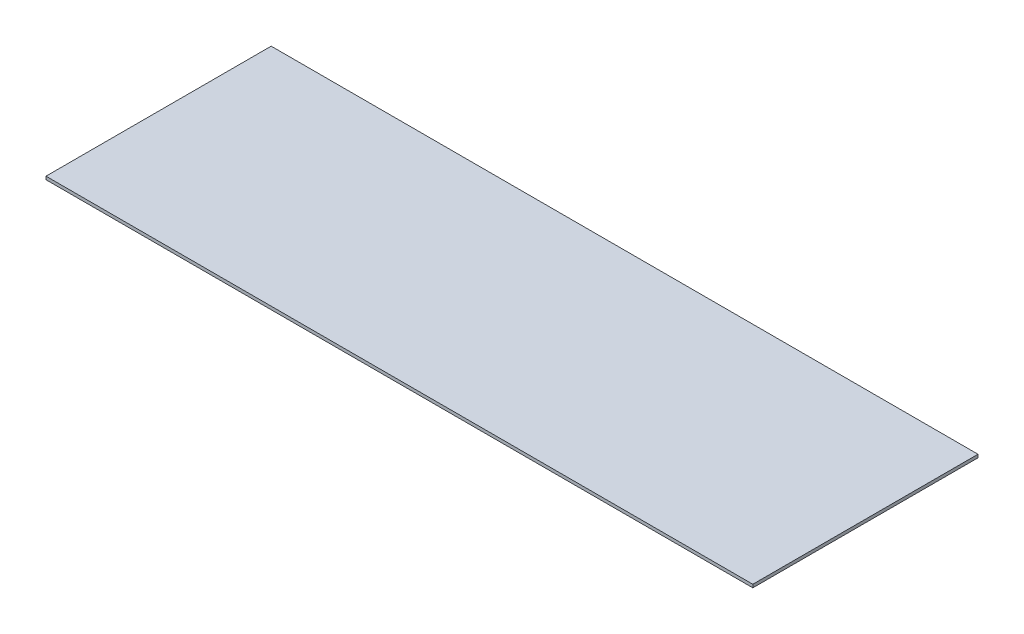
SolidWorks part; units mm, degrees
ref_plane "Front" through (0, 0, 0) normal (0, 0, 1) x (1, 0, 0)
ref_plane "Top" through (0, 0, 0) normal (0, 1, 0) x (1, 0, 0)
ref_plane "Right" through (0, 0, 0) normal (1, 0, 0) x (0, 0, -1)
sketch "Sketch1" plane through (0, 0, 0) normal (0, 1, 0) x (1, 0, 0)
  line L1 (-1087.6487, 331.7391) -> (42.3513, 331.7391)
  line L2 (-1087.6487, 331.7391) -> (-1087.6487, -28.2609)
  line L3 (-1087.6487, -28.2609) -> (42.3513, -28.2609)
  line L4 (42.3513, 331.7391) -> (42.3513, -28.2609)
  dimension "D1" = 1130
  dimension "D2" = 360
extrude "Boss-Extrude1" add sketch "Sketch1" along normal blind 5
